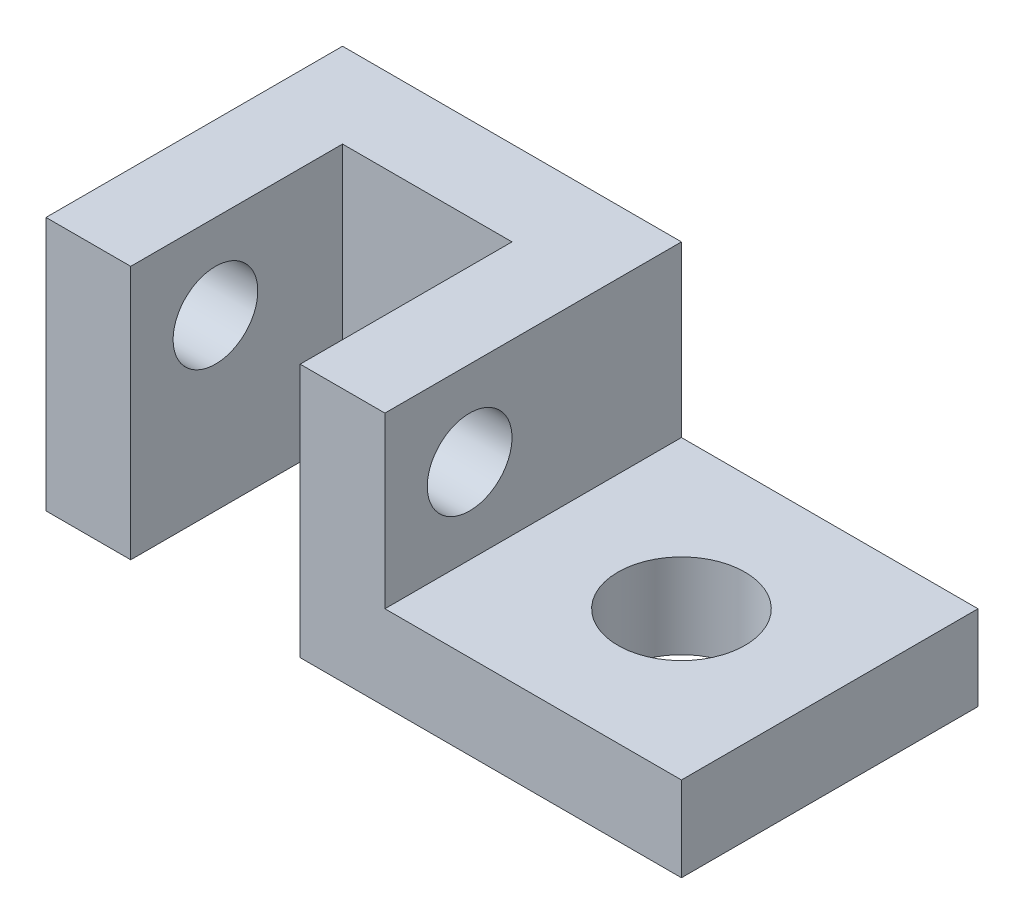
SolidWorks part; units mm, degrees
ref_plane "Front Plane" through (0, 0, 0) normal (0, 0, 1) x (1, 0, 0)
ref_plane "Top Plane" through (0, 0, 0) normal (0, 1, 0) x (1, 0, 0)
ref_plane "Right Plane" through (0, 0, 0) normal (1, 0, 0) x (0, 0, -1)
sketch "Sketch1" plane through (0, 0, 0) normal (0, 1, 0) x (1, 0, 0)
  line L1 (0, 0) -> (75, 0)
  line L2 (0, 0) -> (0, 35)
  line L3 (0, 35) -> (75, 35)
  line L4 (75, 0) -> (75, 35)
  dimension "D1" = 75
  dimension "D2" = 35
extrude "Boss-Extrude1" add sketch "Sketch1" along normal blind 30
sketch "Sketch2" plane through (0, 0, 0) normal (0, 0, 1) x (1, 0, 0)
  line L0 (0, 0) -> (10, 0) construction
  line L1 (0, 0) -> (75, 0) construction
  line L2 (0, 30) -> (75, 30) construction
  line L3 (10, 0) -> (30, 0)
  line L4 (10, 0) -> (10, 30)
  line L5 (10, 30) -> (30, 30)
  line L6 (30, 0) -> (30, 30)
  dimension "D1" = 10
  dimension "D2" = 20
extrude "Cut-Extrude1" cut sketch "Sketch2" against normal blind 25
sketch "Sketch3" plane through (0, 0, 0) normal (0, 0, 1) x (1, 0, 0)
  line L1 (75, 30) -> (40, 30)
  line L2 (75, 30) -> (75, 10)
  line L3 (75, 10) -> (40, 10)
  line L4 (40, 30) -> (40, 10)
  dimension "D1" = 20
  dimension "D2" = 35
extrude "Cut-Extrude2" cut sketch "Sketch3" against normal through all
sketch "Sketch4" plane through (0, 10, 0) normal (0, 1, 0) x (1, 0, 0)
  line L0 (75, 17.5) -> (57.5, 17.5) construction
  line L1 (75, 35) -> (75, 0) construction
  circle A0 centre (57.5, 17.5) radius 7.5
  dimension "D2" = 15
  dimension "D1" = 17.5
extrude "Cut-Extrude3" cut sketch "Sketch4" against normal through all contours A0
sketch "Sketch5" plane through (0, 0, 0) normal (-1, 0, 0) x (0, 0, 1)
  line L0 (0, 30) -> (0, 20) construction
  line L1 (0, 30) -> (0, 0) construction
  line L2 (0, 20) -> (-10, 20) construction
  circle A0 centre (-10, 20) radius 5
  dimension "D3" = 10
  dimension "D1" = 10
  dimension "D2" = 10
extrude "Cut-Extrude4" cut sketch "Sketch5" against normal through all contours A0
